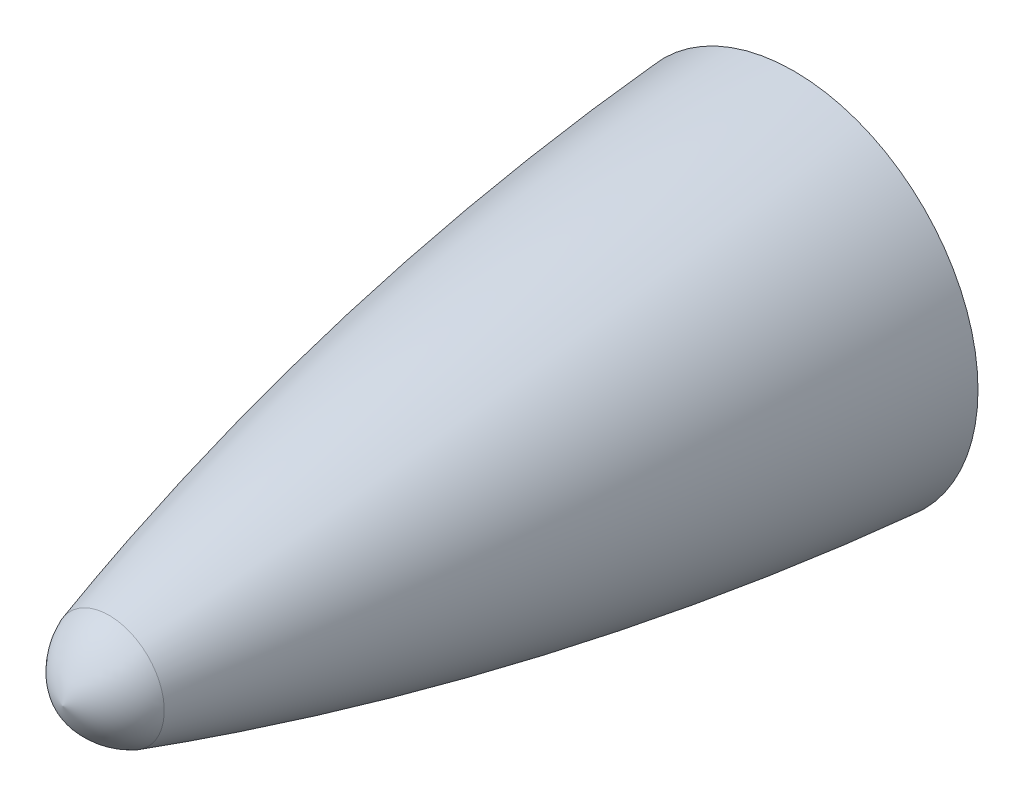
SolidWorks part; units mm, degrees
ref_plane "Front Plane" through (0, 0, 0) normal (0, 0, 1) x (1, 0, 0)
ref_plane "Top Plane" through (0, 0, 0) normal (0, 1, 0) x (1, 0, 0)
ref_plane "Right Plane" through (0, 0, 0) normal (1, 0, 0) x (0, 0, -1)
sketch "Sketch2" plane through (0, 0, 0) normal (1, 0, 0) x (0, 0, -1)
  line L0 (-12, 0) -> (-35.8411, 0)
  line L2 (-12, 0) -> (-12, 6)
  arc A0 (-12, 6) -> (-34.3224, 1.7972) centre (-4.0388, -97.6664) ccw
  arc A1 (-34.3224, 1.7972) -> (-35.8411, 0) centre (-33.2881, -0.6172) ccw
revolve "Revolve1" add sketch "Sketch2" angle 360 about L0
